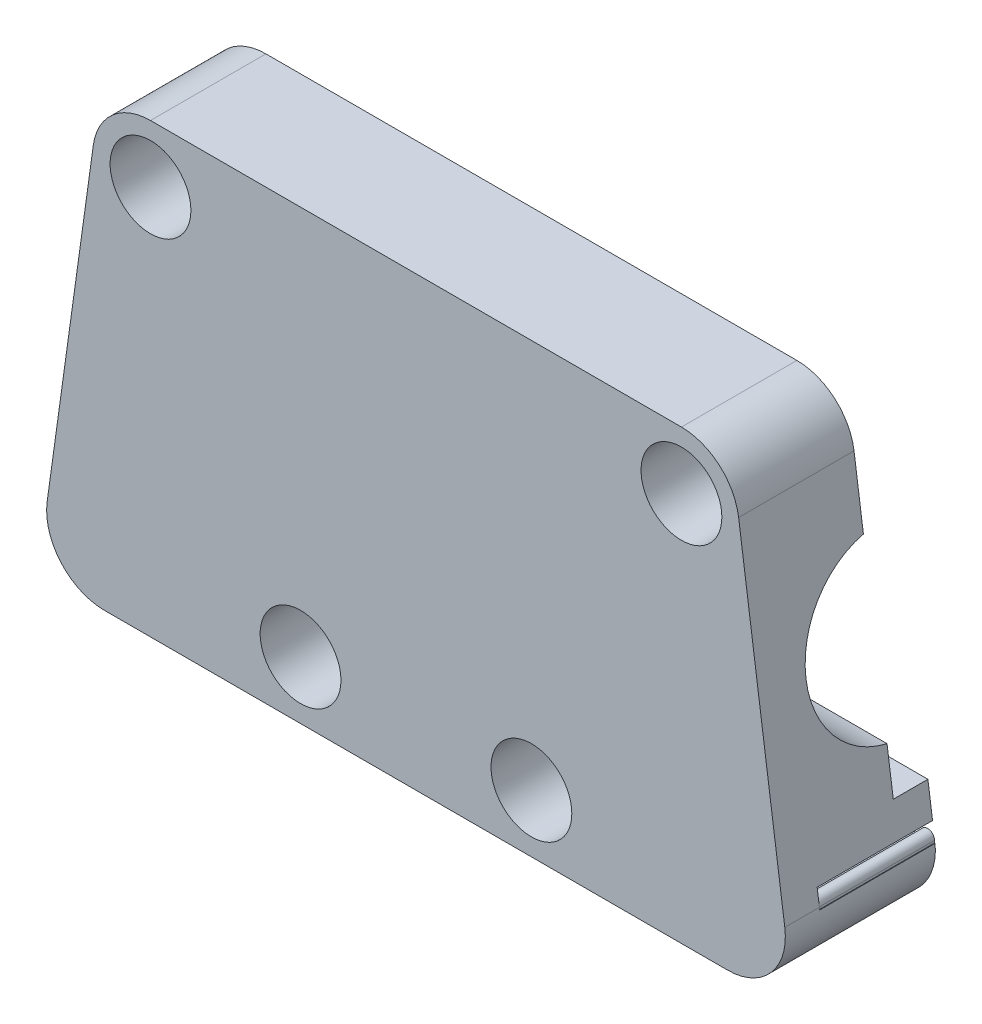
SolidWorks part; units mm, degrees
ref_plane "Front Plane" through (0, 0, 0) normal (0, 0, 1) x (1, 0, 0)
ref_plane "Top Plane" through (0, 0, 0) normal (0, 1, 0) x (1, 0, 0)
ref_plane "Right Plane" through (0, 0, 0) normal (1, 0, 0) x (0, 0, -1)
sketch "Sketch1" plane through (0, 0, 0) normal (0, 0, 1) x (1, 0, 0)
  line L1 (-23, 12.5) -> (23, 12.5) construction
  line L2 (0, -16.25) -> (0, 12.5) construction
  line L3 (-27, -21.25) -> (27, -21.25)
  line L4 (31.9523, -15.561) -> (27.9523, 13.189)
  line L5 (23, 17.5) -> (-23, 17.5)
  line L6 (-27.9523, 13.189) -> (-31.9523, -15.561)
  line L7 (27, -16.25) -> (-27, -16.25) construction
  circle A0 centre (-10, -16.25) radius 2
  circle A1 centre (10, -16.25) radius 2
  circle A2 centre (23, 12.5) radius 2
  circle A3 centre (-23, 12.5) radius 2
  arc A6 (23, 17.5) -> (27.9523, 13.189) centre (23, 12.5) cw
  arc A8 (-23, 17.5) -> (-27.9523, 13.189) centre (-23, 12.5) ccw
  arc A9 (-27, -21.25) -> (-31.9523, -15.561) centre (-27, -16.25) cw
  arc A10 (27, -21.25) -> (31.9523, -15.561) centre (27, -16.25) ccw
  point P11 (0, -16.25)
  dimension "D4" = 4
  dimension "D5" = 4
  dimension "D6" = 4
  dimension "D7" = 4
  dimension "D8" = 5
  dimension "D9" = 5
  dimension "D10" = 5
  dimension "D11" = 5
  dimension "D1" = 20
  dimension "D2" = 46
  dimension "D3" = 28.75
  dimension "D12" = 12.5
  dimension "D13" = 54
extrude "Boss-Extrude1" add sketch "Sketch1" along normal blind 10
sketch "Sketch2" plane through (0, 0, 0) normal (1, 0, 0) x (0, 0, -1)
  line L0 (0, 13.189) -> (0, -15.561) construction
  line L1 (0, 0) -> (1.5, 0) construction
  circle A0 centre (1.5, 0) radius 5
  dimension "D1" = 10
  dimension "D2" = 1.5
extrude "Cut-Extrude1" cut sketch "Sketch2" against normal through all both and the other way through all
ref_plane "Plane1" through (15, 0, 0) normal (1, 0, 0) x (0, 0, -1)
sketch "Sketch3" plane through (15, 0, 0) normal (1, 0, 0) x (0, 0, -1)
  circle A0 centre (1.5, 0) radius 7.5
  dimension "D1" = 15
  dimension "D2" = 1.5
extrude "Cut-Extrude2" cut sketch "Sketch3" along normal blind 16
mirror "Mirror1" about plane through (0, 0, 0) normal (1, 0, 0) of "Cut-Extrude2"
sketch "Sketch4" plane through (0, 0, 10) normal (0, 0, 1) x (1, 0, 0)
  circle A0 centre (10, -16.25) radius 3.5
  circle A1 centre (-10, -16.25) radius 3.5
  circle A2 centre (23, 12.5) radius 3.5
  circle A3 centre (-23, 12.5) radius 3.5
  dimension "D1" = 7
  dimension "D2" = 7
  dimension "D3" = 7
  dimension "D4" = 7
extrude "Cut-Extrude3" cut sketch "Sketch4" against normal blind 8
sketch "Sketch5" plane through (0, 0, 0) normal (0, 0, -1) x (-1, 0, 0)
  line L0 (31.5376, -14.15) -> (-31.5376, -14.15)
  line L1 (31.9749, -15.75) -> (-31.9749, -15.75)
  line L2 (-31.9523, -15.561) -> (-30.8097, -7.3485) construction
  line L3 (27, -21.25) -> (-27, -21.25) construction
  line L4 (-25.8734, -14.95) -> (-31.8673, -14.95) construction
  line L7 (-31.9749, -15.75) -> (-31.9749, -14.15)
  line L8 (-31.9749, -14.15) -> (-31.5376, -14.15)
  line L9 (31.9749, -15.75) -> (31.9749, -14.15)
  line L10 (31.9749, -14.15) -> (31.5376, -14.15)
  line L11 (-31.9249, -15.75) -> (-31.9249, -15.55)
  line L12 (-30.7249, -15.75) -> (-30.7249, -15.55)
  arc A0 (27, -21.25) -> (31.9523, -15.561) centre (27, -16.25) ccw construction
  arc A1 (-31.9523, -15.561) -> (-27, -21.25) centre (-27, -16.25) ccw construction
  arc A2 (-31.9249, -15.55) -> (-30.7249, -15.55) centre (-31.3249, -15.55) cw
  dimension "D1" = 0.8
  dimension "D2" = 0.05
  dimension "D3" = 1.6
  dimension "D4" = 5.5
  dimension "D7" = 0.2
  dimension "D8" = 1.2
sketch "Sketch6" plane through (0, 0, 0) normal (0, 0, -1) x (-1, 0, 0)
  line L0 (31.5376, -14.15) -> (-31.5376, -14.15) construction
  line L1 (-31.9749, -15.75) -> (-20.5891, -15.75)
  line L2 (-31.9749, -15.75) -> (-31.9749, -14.15)
  line L3 (-31.9749, -14.15) -> (-19.9749, -14.15)
  line L5 (20.5891, -15.75) -> (14.4808, -21.25)
  line L6 (31.9749, -15.75) -> (20.5891, -15.75)
  line L7 (31.9749, -15.75) -> (31.9749, -14.15)
  line L8 (31.9749, -14.15) -> (19.9749, -14.15)
  line L10 (27, -21.25) -> (-27, -21.25) construction
  line L11 (19.9749, -14.15) -> (12.0896, -21.25)
  line L12 (-19.9749, -14.15) -> (-12.0896, -21.25)
  line L13 (14.4808, -21.25) -> (12.0896, -21.25)
  line L14 (-20.5891, -15.75) -> (-14.4808, -21.25)
  line L15 (-14.4808, -21.25) -> (-12.0896, -21.25)
  line L16 (31.9749, -15.75) -> (-31.9749, -15.75) construction
  dimension "D1" = 12
  dimension "D2" = 12
  dimension "D3" = 1.6
  dimension "D4" = 1.6
  dimension "D5" = 138
  dimension "D6" = 138
extrude "Cut-Extrude4" cut sketch "Sketch6" against normal blind 7
sketch "Sketch7" plane through (0, 0, 10) normal (0, 0, 1) x (1, 0, 0)
  line L5 (-31.9749, -15.75) -> (31.9749, -15.75) construction
  line L6 (30.7249, -15.75) -> (30.7249, -15.55) construction
  line L7 (31.9249, -15.75) -> (31.9249, -15.55) construction
  line L8 (30.7249, -15.75) -> (31.9249, -15.75)
  line L9 (30.7249, -15.75) -> (30.7249, -15.55)
  line L10 (31.9249, -15.75) -> (31.9249, -15.55)
  arc A2 (31.9249, -15.55) -> (30.7249, -15.55) centre (31.3249, -15.55) ccw construction
  arc A3 (31.9249, -15.55) -> (30.7249, -15.55) centre (31.3249, -15.55) ccw
extrude "Boss-Extrude2" add sketch "Sketch7" along normal up to next from surface
pattern_linear "LPattern1" count 6 spacing 2 along (-1, 0, 0) of "Boss-Extrude2"
pattern_linear "LPattern2" count 2 spacing 52.6 along (-1, 0, 0) of "LPattern1", "Boss-Extrude2"
fillet "Fillet1" radius 5 2 edges at (-12.0896, -21.25, 3.5) (12.0896, -21.25, 3.5)
fillet "Fillet2" radius 1 2 edges at (14.4808, -21.25, 3.5) (-14.4808, -21.25, 3.5)
sketch "Sketch8" plane through (0, 0, 0) normal (0, 0, -1) x (-1, 0, 0)
  line L0 (-27, -21.25) -> (-17.0858, -21.25) construction
  line L1 (-16.4167, -19.5069) -> (-20.5891, -15.75) construction
  line L2 (-20.5891, -15.75) -> (-20.7249, -15.75) construction
  line L3 (-20.7249, -15.75) -> (-20.7249, -15.55) construction
  line L4 (-21.9249, -15.55) -> (-21.9249, -15.75) construction
  line L5 (-21.9249, -15.75) -> (-22.7249, -15.75) construction
  line L6 (-22.7249, -15.75) -> (-22.7249, -15.55) construction
  line L7 (-23.9249, -15.55) -> (-23.9249, -15.75) construction
  line L8 (-23.9249, -15.75) -> (-24.7249, -15.75) construction
  line L9 (-24.7249, -15.75) -> (-24.7249, -15.55) construction
  line L10 (-25.9249, -15.55) -> (-25.9249, -15.75) construction
  line L11 (-25.9249, -15.75) -> (-26.7249, -15.75) construction
  line L12 (-26.7249, -15.75) -> (-26.7249, -15.55) construction
  line L13 (-27.9249, -15.55) -> (-27.9249, -15.75) construction
  line L14 (-27.9249, -15.75) -> (-28.7249, -15.75) construction
  line L15 (-28.7249, -15.75) -> (-28.7249, -15.55) construction
  line L16 (-29.9249, -15.55) -> (-29.9249, -15.75) construction
  line L17 (-29.9249, -15.75) -> (-30.7249, -15.75) construction
  line L18 (-30.7249, -15.75) -> (-30.7249, -15.55) construction
  line L19 (-31.9249, -15.55) -> (-31.9249, -15.75) construction
  line L20 (-31.9249, -15.75) -> (-31.9749, -15.75) construction
  line L21 (20.5891, -15.75) -> (16.4167, -19.5069) construction
  line L22 (17.0858, -21.25) -> (27, -21.25) construction
  line L23 (31.9749, -15.75) -> (31.8751, -15.75) construction
  line L24 (31.8751, -15.75) -> (31.8751, -15.55) construction
  line L25 (30.6751, -15.55) -> (30.6751, -15.75) construction
  line L26 (30.6751, -15.75) -> (29.8751, -15.75) construction
  line L27 (29.8751, -15.75) -> (29.8751, -15.55) construction
  line L28 (28.6751, -15.55) -> (28.6751, -15.75) construction
  line L29 (28.6751, -15.75) -> (27.8751, -15.75) construction
  line L30 (27.8751, -15.75) -> (27.8751, -15.55) construction
  line L31 (26.6751, -15.55) -> (26.6751, -15.75) construction
  line L32 (26.6751, -15.75) -> (25.8751, -15.75) construction
  line L33 (25.8751, -15.75) -> (25.8751, -15.55) construction
  line L34 (24.6751, -15.55) -> (24.6751, -15.75) construction
  line L35 (24.6751, -15.75) -> (23.8751, -15.75) construction
  line L36 (23.8751, -15.75) -> (23.8751, -15.55) construction
  line L37 (22.6751, -15.55) -> (22.6751, -15.75) construction
  line L38 (22.6751, -15.75) -> (21.8751, -15.75) construction
  line L39 (21.8751, -15.75) -> (21.8751, -15.55) construction
  line L40 (20.6751, -15.55) -> (20.6751, -15.75) construction
  line L41 (20.6751, -15.75) -> (20.5891, -15.75) construction
  line L42 (-27, -21.25) -> (-17.0858, -21.25)
  line L43 (-16.4167, -19.5069) -> (-20.5891, -15.75)
  line L44 (-20.5891, -15.75) -> (-20.7249, -15.75)
  line L45 (-20.7249, -15.75) -> (-20.7249, -15.55)
  line L46 (-21.9249, -15.55) -> (-21.9249, -15.75)
  line L47 (-21.9249, -15.75) -> (-22.7249, -15.75)
  line L48 (-22.7249, -15.75) -> (-22.7249, -15.55)
  line L49 (-23.9249, -15.55) -> (-23.9249, -15.75)
  line L50 (-23.9249, -15.75) -> (-24.7249, -15.75)
  line L51 (-24.7249, -15.75) -> (-24.7249, -15.55)
  line L52 (-25.9249, -15.55) -> (-25.9249, -15.75)
  line L53 (-25.9249, -15.75) -> (-26.7249, -15.75)
  line L54 (-26.7249, -15.75) -> (-26.7249, -15.55)
  line L55 (-27.9249, -15.55) -> (-27.9249, -15.75)
  line L56 (-27.9249, -15.75) -> (-28.7249, -15.75)
  line L57 (-28.7249, -15.75) -> (-28.7249, -15.55)
  line L58 (-29.9249, -15.55) -> (-29.9249, -15.75)
  line L59 (-29.9249, -15.75) -> (-30.7249, -15.75)
  line L60 (-30.7249, -15.75) -> (-30.7249, -15.55)
  line L61 (-31.9249, -15.55) -> (-31.9249, -15.75)
  line L62 (-31.9249, -15.75) -> (-31.9749, -15.75)
  line L63 (20.5891, -15.75) -> (16.4167, -19.5069)
  line L64 (17.0858, -21.25) -> (27, -21.25)
  line L65 (31.9749, -15.75) -> (31.8751, -15.75)
  line L66 (31.8751, -15.75) -> (31.8751, -15.55)
  line L67 (30.6751, -15.55) -> (30.6751, -15.75)
  line L68 (30.6751, -15.75) -> (29.8751, -15.75)
  line L69 (29.8751, -15.75) -> (29.8751, -15.55)
  line L70 (28.6751, -15.55) -> (28.6751, -15.75)
  line L71 (28.6751, -15.75) -> (27.8751, -15.75)
  line L72 (27.8751, -15.75) -> (27.8751, -15.55)
  line L73 (26.6751, -15.55) -> (26.6751, -15.75)
  line L74 (26.6751, -15.75) -> (25.8751, -15.75)
  line L75 (25.8751, -15.75) -> (25.8751, -15.55)
  line L76 (24.6751, -15.55) -> (24.6751, -15.75)
  line L77 (24.6751, -15.75) -> (23.8751, -15.75)
  line L78 (23.8751, -15.75) -> (23.8751, -15.55)
  line L79 (22.6751, -15.55) -> (22.6751, -15.75)
  line L80 (22.6751, -15.75) -> (21.8751, -15.75)
  line L81 (21.8751, -15.75) -> (21.8751, -15.55)
  line L82 (20.6751, -15.55) -> (20.6751, -15.75)
  line L83 (20.6751, -15.75) -> (20.5891, -15.75)
  line L84 (-19.9749, -14.15) -> (-31.756, -14.15) construction
  line L85 (-13.5159, -19.9657) -> (-19.9749, -14.15) construction
  line L86 (10.1703, -21.25) -> (-10.1703, -21.25) construction
  line L87 (19.9749, -14.15) -> (13.5159, -19.9657) construction
  line L88 (31.756, -14.15) -> (19.9749, -14.15) construction
  line L89 (-19.9749, -14.15) -> (-31.756, -14.15)
  line L90 (-13.5159, -19.9657) -> (-19.9749, -14.15)
  line L91 (10.1703, -21.25) -> (-10.1703, -21.25)
  line L92 (19.9749, -14.15) -> (13.5159, -19.9657)
  line L93 (31.756, -14.15) -> (19.9749, -14.15)
  line L94 (-31.756, -14.15) -> (-30.8097, -7.3485) construction
  line L95 (30.8097, -7.3485) -> (31.756, -14.15) construction
  line L96 (-31.756, -14.15) -> (-30.8097, -7.3485)
  line L97 (30.8097, -7.3485) -> (31.756, -14.15)
  line L98 (31.3525, -11.25) -> (-31.3525, -11.25)
  arc A0 (-17.0858, -21.25) -> (-16.4167, -19.5069) centre (-17.0858, -20.25) ccw construction
  arc A1 (-20.7249, -15.55) -> (-21.9249, -15.55) centre (-21.3249, -15.55) ccw construction
  arc A2 (-22.7249, -15.55) -> (-23.9249, -15.55) centre (-23.3249, -15.55) ccw construction
  arc A3 (-24.7249, -15.55) -> (-25.9249, -15.55) centre (-25.3249, -15.55) ccw construction
  arc A4 (-26.7249, -15.55) -> (-27.9249, -15.55) centre (-27.3249, -15.55) ccw construction
  arc A5 (-28.7249, -15.55) -> (-29.9249, -15.55) centre (-29.3249, -15.55) ccw construction
  arc A6 (-30.7249, -15.55) -> (-31.9249, -15.55) centre (-31.3249, -15.55) ccw construction
  arc A7 (-31.9749, -15.75) -> (-27, -21.25) centre (-27, -16.25) ccw construction
  arc A8 (16.4167, -19.5069) -> (17.0858, -21.25) centre (17.0858, -20.25) ccw construction
  arc A9 (27, -21.25) -> (31.9749, -15.75) centre (27, -16.25) ccw construction
  arc A10 (31.8751, -15.55) -> (30.6751, -15.55) centre (31.2751, -15.55) ccw construction
  arc A11 (29.8751, -15.55) -> (28.6751, -15.55) centre (29.2751, -15.55) ccw construction
  arc A12 (27.8751, -15.55) -> (26.6751, -15.55) centre (27.2751, -15.55) ccw construction
  arc A13 (25.8751, -15.55) -> (24.6751, -15.55) centre (25.2751, -15.55) ccw construction
  arc A14 (23.8751, -15.55) -> (22.6751, -15.55) centre (23.2751, -15.55) ccw construction
  arc A15 (21.8751, -15.55) -> (20.6751, -15.55) centre (21.2751, -15.55) ccw construction
  arc A16 (-17.0858, -21.25) -> (-16.4167, -19.5069) centre (-17.0858, -20.25) ccw
  arc A17 (-20.7249, -15.55) -> (-21.9249, -15.55) centre (-21.3249, -15.55) ccw
  arc A18 (-22.7249, -15.55) -> (-23.9249, -15.55) centre (-23.3249, -15.55) ccw
  arc A19 (-24.7249, -15.55) -> (-25.9249, -15.55) centre (-25.3249, -15.55) ccw
  arc A20 (-26.7249, -15.55) -> (-27.9249, -15.55) centre (-27.3249, -15.55) ccw
  arc A21 (-28.7249, -15.55) -> (-29.9249, -15.55) centre (-29.3249, -15.55) ccw
  arc A22 (-30.7249, -15.55) -> (-31.9249, -15.55) centre (-31.3249, -15.55) ccw
  arc A23 (-31.9749, -15.75) -> (-27, -21.25) centre (-27, -16.25) ccw
  arc A24 (16.4167, -19.5069) -> (17.0858, -21.25) centre (17.0858, -20.25) ccw
  arc A25 (27, -21.25) -> (31.9749, -15.75) centre (27, -16.25) ccw
  arc A26 (31.8751, -15.55) -> (30.6751, -15.55) centre (31.2751, -15.55) ccw
  arc A27 (29.8751, -15.55) -> (28.6751, -15.55) centre (29.2751, -15.55) ccw
  arc A28 (27.8751, -15.55) -> (26.6751, -15.55) centre (27.2751, -15.55) ccw
  arc A29 (25.8751, -15.55) -> (24.6751, -15.55) centre (25.2751, -15.55) ccw
  arc A30 (23.8751, -15.55) -> (22.6751, -15.55) centre (23.2751, -15.55) ccw
  arc A31 (21.8751, -15.55) -> (20.6751, -15.55) centre (21.2751, -15.55) ccw
  arc A32 (-13.5159, -19.9657) -> (-10.1703, -21.25) centre (-10.1703, -16.25) ccw construction
  arc A33 (10.1703, -21.25) -> (13.5159, -19.9657) centre (10.1703, -16.25) ccw construction
  arc A34 (-13.5159, -19.9657) -> (-10.1703, -21.25) centre (-10.1703, -16.25) ccw
  arc A35 (10.1703, -21.25) -> (13.5159, -19.9657) centre (10.1703, -16.25) ccw
  circle A36 centre (-10, -16.25) radius 2 construction
  circle A37 centre (10, -16.25) radius 2 construction
  circle A38 centre (-10, -16.25) radius 2
  circle A39 centre (10, -16.25) radius 2
  circle M3 centre (-10, -16.25) radius 2
  circle M4 centre (10, -16.25) radius 2
  line M5 (-10.1703, -21.25) -> (10.1703, -21.25)
  arc M6 (10.1703, -21.25) -> (13.5159, -19.9657) centre (10.1703, -16.25) ccw
  line M7 (13.5159, -19.9657) -> (19.9749, -14.15)
  line M8 (19.9749, -14.15) -> (31.756, -14.15)
  line M9 (31.756, -14.15) -> (30.8097, -7.3485)
  line M16 (-31.756, -14.15) -> (-19.9749, -14.15)
  line M17 (-19.9749, -14.15) -> (-13.5159, -19.9657)
  arc M18 (-13.5159, -19.9657) -> (-10.1703, -21.25) centre (-10.1703, -16.25) ccw
  dimension "D1" = 10
extrude "Boss-Extrude3" add sketch "Sketch8" along normal blind 3 contours L62 A23 L42 A16 L43 L44 L45 A17 L46 L47 L48 A18 L49 L50 L51 A19 L52 L53 L54 A20 L55 L56 L57 A21 L58 L59 L60 A22 L61 | L98 L96 M9 M16 M17 M18 M5 M6 M7 M8 M4 M3 | L81 A31 L82 L83 L63 A24 L64 A25 L65 L66 A26 L67 L68 L69 A27 L70 L71 L72 A28 L73 L74 L75 A29 L76 L77 L78 A30 L79 L80
